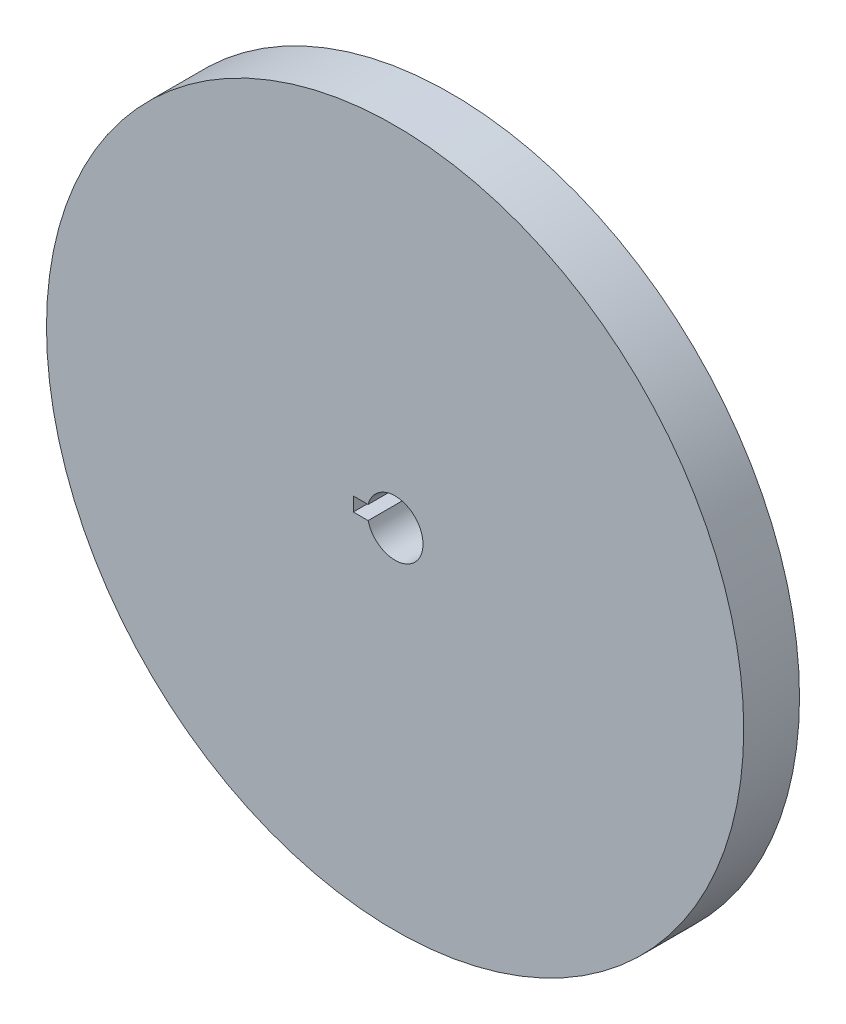
SolidWorks part; units mm, degrees
ref_plane "Front Plane" through (0, 0, 0) normal (0, 0, 1) x (1, 0, 0)
ref_plane "Top Plane" through (0, 0, 0) normal (0, 1, 0) x (1, 0, 0)
ref_plane "Right Plane" through (0, 0, 0) normal (1, 0, 0) x (0, 0, -1)
sketch "Sketch1" plane through (0, 0, 0) normal (0, 0, 1) x (1, 0, 0)
  circle A0 centre (0, 0) radius 125
  dimension "D1" = 250
extrude "Boss-Extrude1" add sketch "Sketch1" along normal blind 20
sketch "Sketch2" plane through (0, 0, 20) normal (0, 0, 1) x (1, 0, 0)
  line L1 (-9.6825, 2.5) -> (-15, 2.5)
  line L3 (-9.6825, -2.5) -> (-15, -2.5)
  line L4 (-15, 2.5) -> (-15, -2.5)
  line L5 (-5, 2.5) -> (-15, -2.5) construction
  line L6 (-5, -2.5) -> (-15, 2.5) construction
  arc A0 (-9.6825, -2.5) -> (-9.6825, 2.5) centre (0, 0) ccw
  point P3 (-10, 0)
  dimension "D1" = 20
  dimension "D2" = 10
  dimension "D3" = 15
  dimension "5" = 5
  dimension "D4" = 5.3175
extrude "Cut-Extrude1" cut sketch "Sketch2" against normal through all
